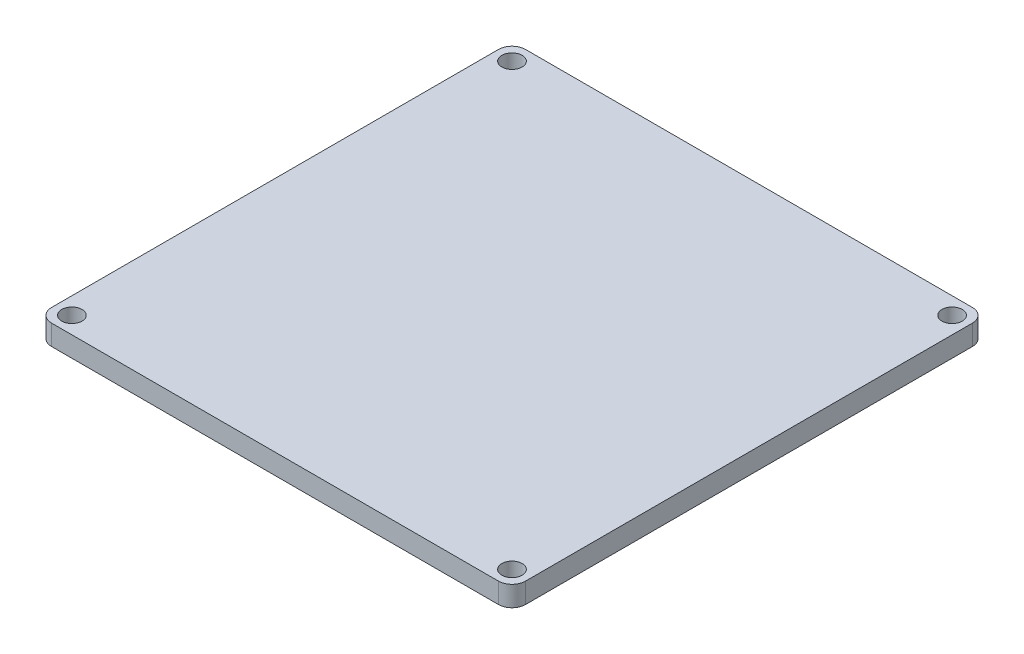
SolidWorks part; units mm, degrees
ref_plane "Front Plane" through (0, 0, 0) normal (0, 0, 1) x (1, 0, 0)
ref_plane "Top Plane" through (0, 0, 0) normal (0, 1, 0) x (1, 0, 0)
ref_plane "Right Plane" through (0, 0, 0) normal (1, 0, 0) x (0, 0, -1)
sketch "Sketch1" plane through (0, 0, 0) normal (0, 1, 0) x (1, 0, 0)
  line L1 (-35, 35) -> (35, 35)
  line L2 (-35, 35) -> (-35, -35)
  line L3 (-35, -35) -> (35, -35)
  line L4 (35, 35) -> (35, -35)
  line L5 (-35, 35) -> (35, -35) construction
  line L6 (-35, -35) -> (35, 35) construction
  circle A0 centre (-32.5, 32.5) radius 1.5
  circle A1 centre (32.5, 32.5) radius 1.5
  circle A2 centre (32.5, -32.5) radius 1.5
  circle A3 centre (-32.5, -32.5) radius 1.5
  point P0 (0, 0)
  dimension "D4" = 3
  dimension "D1" = 70
  dimension "D2" = 70
  dimension "D3" = 2.5
  dimension "D5" = 2
extrude "Boss-Extrude1" add sketch "Sketch1" along normal blind 3
fillet "Fillet1" radius 2 4 edges at (-35, 1.5, -35) (35, 1.5, -35) (35, 1.5, 35) (-35, 1.5, 35)
